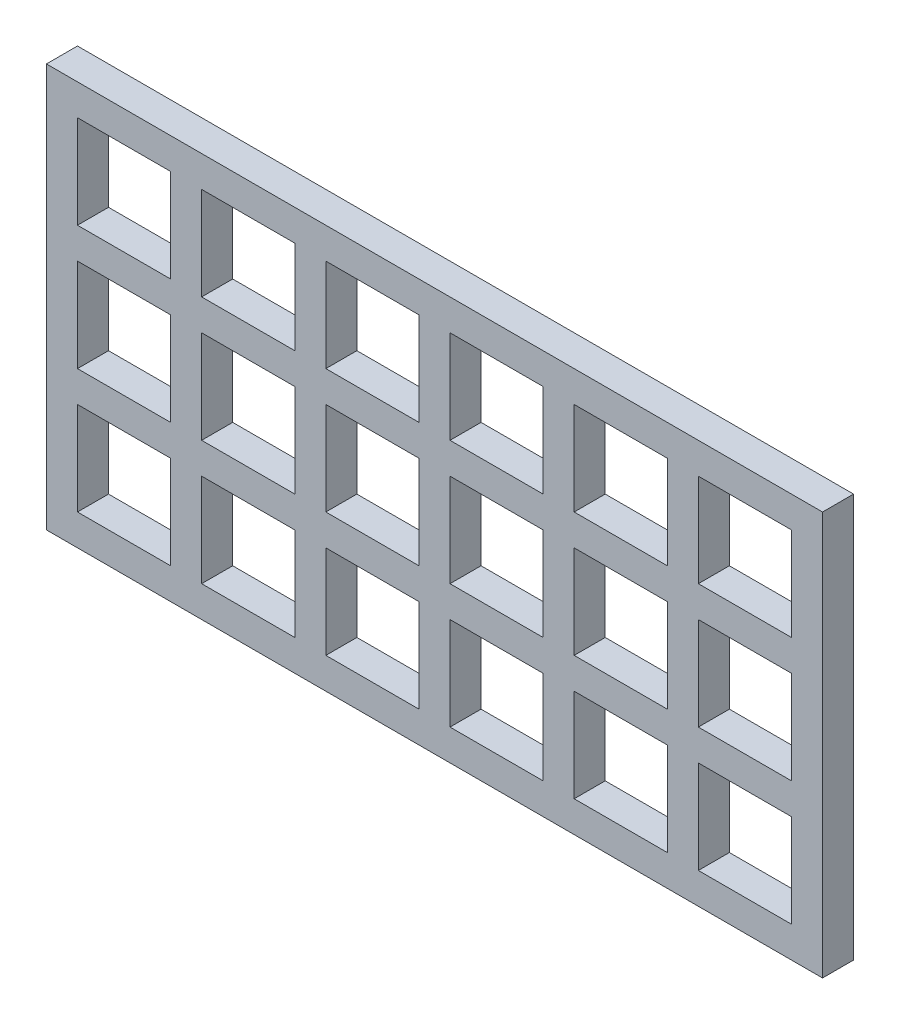
SolidWorks part; units mm, degrees
ref_plane "前视基准面" through (0, 0, 0) normal (0, 0, 1) x (1, 0, 0)
ref_plane "上视基准面" through (0, 0, 0) normal (0, 1, 0) x (1, 0, 0)
ref_plane "右视基准面" through (0, 0, 0) normal (1, 0, 0) x (0, 0, -1)
other "Configuration Table"
sketch "草图1" plane through (0, 0, 0) normal (0, 0, 1) x (1, 0, 0)
  line L1 (-62.5, 32.5) -> (62.5, 32.5)
  line L2 (-62.5, 32.5) -> (-62.5, -32.5)
  line L3 (-62.5, -32.5) -> (62.5, -32.5)
  line L4 (62.5, 32.5) -> (62.5, -32.5)
  line L5 (-62.5, 32.5) -> (62.5, -32.5) construction
  line L6 (-62.5, -32.5) -> (62.5, 32.5) construction
  point P0 (0, 0)
  dimension "D1" = 65
extrude "凸台-拉伸1" add sketch "草图1" along normal blind 5
sketch "草图2" plane through (0, 0, 5) normal (0, 0, 1) x (1, 0, 0)
  line L1 (-62.5, 32.5) -> (-57.5, 32.5) construction
  line L2 (-62.5, 32.5) -> (-62.5, 27.5) construction
  line L3 (-62.5, 27.5) -> (-57.5, 27.5) construction
  line L4 (-57.5, 32.5) -> (-57.5, 27.5) construction
  line L5 (-62.5, 32.5) -> (-57.5, 27.5) construction
  line L6 (-62.5, 27.5) -> (-57.5, 32.5) construction
  line L7 (-57.5, 27.5) -> (-42.5, 27.5)
  line L8 (-57.5, 27.5) -> (-57.5, 12.5)
  line L9 (-57.5, 12.5) -> (-42.5, 12.5)
  line L10 (-42.5, 27.5) -> (-42.5, 12.5)
  line L11 (-57.5, 27.5) -> (-42.5, 12.5) construction
  line L12 (-57.5, 12.5) -> (-42.5, 27.5) construction
  point P4 (-60, 30)
  point P9 (-50, 20)
  dimension "D1" = 5
  dimension "D2" = 5
  dimension "D3" = 15
  dimension "D4" = 15
extrude "切除-拉伸1" cut sketch "草图2" against normal blind 5
pattern_linear "阵列(线性)1" count 6 spacing 20 along (1, 0, 0) count 3 spacing 20 along (0, -1, 0) of "切除-拉伸1"
